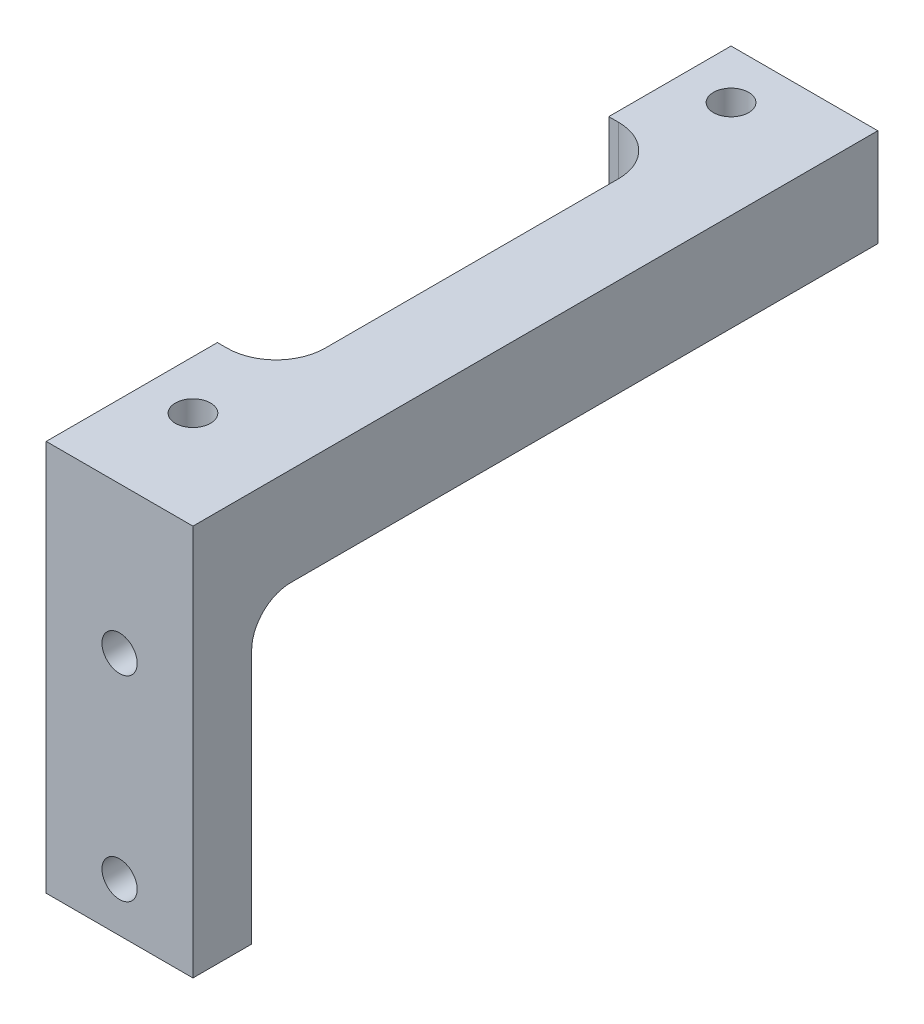
SolidWorks part; units mm, degrees
ref_plane "Front Plane" through (0, 0, 0) normal (0, 0, 1) x (1, 0, 0)
ref_plane "Top Plane" through (0, 0, 0) normal (0, 1, 0) x (1, 0, 0)
ref_plane "Right Plane" through (0, 0, 0) normal (1, 0, 0) x (0, 0, -1)
sketch "Sketch2" plane through (0, 0, 0) normal (0, 0, 1) x (1, 0, 0)
  line L1 (-23.8125, -12.7) -> (23.8125, -12.7)
  line L2 (-23.8125, -12.7) -> (-23.8125, 12.7)
  line L3 (-23.8125, 12.7) -> (23.8125, 12.7)
  line L4 (23.8125, -12.7) -> (23.8125, 12.7)
  line L5 (-23.8125, -12.7) -> (23.8125, 12.7) construction
  line L6 (-23.8125, 12.7) -> (23.8125, -12.7) construction
  point P0 (0, 0)
  dimension "D1" = 25.4
  dimension "D2" = 47.625
extrude "Boss-Extrude1" add sketch "Sketch2" along normal blind 44.45
sketch "Sketch3" plane through (0, 12.7, 0) normal (0, 1, 0) x (1, 0, 0)
  line L0 (0, 0) -> (0, -44.45) construction
  line L1 (23.8125, -44.45) -> (-23.8125, -44.45) construction
  line L2 (23.8125, 0) -> (-23.8125, 0) construction
  line L3 (-14.2875, -44.45) -> (14.2875, -44.45)
  line L4 (-14.2875, -44.45) -> (-14.2875, 0)
  line L5 (-14.2875, 0) -> (14.2875, 0)
  line L6 (14.2875, -44.45) -> (14.2875, 0)
  line L7 (-14.2875, -44.45) -> (14.2875, 0) construction
  line L8 (-14.2875, 0) -> (14.2875, -44.45) construction
  line L9 (23.8125, -44.45) -> (23.8125, 0) construction
  point P5 (0, -22.225)
  dimension "D1" = 9.525
extrude "Cut-Extrude1" cut sketch "Sketch3" against normal through all
sketch "Sketch4" plane through (-23.8125, 0, 0) normal (-1, 0, 0) x (0, 0, 1)
  line L0 (44.45, 12.7) -> (0, 12.7) construction
  line L1 (0, -12.7) -> (40.64, -12.7)
  line L2 (0, -12.7) -> (0, 6.35)
  line L3 (0, 6.35) -> (40.64, 6.35)
  line L4 (40.64, -12.7) -> (40.64, 6.35)
  line L5 (44.45, 12.7) -> (44.45, -12.7) construction
  dimension "D1" = 6.35
  dimension "D2" = 3.81
extrude "Cut-Extrude2" cut sketch "Sketch4" against normal through all
fillet "Fillet1" radius 2.54 1 edges at (19.05, 6.35, 40.64)
fillet "Fillet2" radius 2.54 1 edges at (-19.05, 6.35, 40.64)
sketch "Sketch5" plane through (0, 0, 44.45) normal (0, 0, 1) x (1, 0, 0)
  line L0 (-19.05, 12.7) -> (-19.05, -12.7) construction
  line L3 (-14.2875, 12.7) -> (-23.8125, 12.7) construction
  line L6 (-23.8125, -12.7) -> (-14.2875, -12.7) construction
  line L7 (19.05, -12.7) -> (19.05, 12.7) construction
  line L8 (14.2875, -12.7) -> (23.8125, -12.7) construction
  line L9 (23.8125, 12.7) -> (14.2875, 12.7) construction
  circle A2 centre (-19.05, -9.525) radius 1.143
  circle A3 centre (-19.05, 3.175) radius 1.143
  circle A4 centre (19.05, -9.525) radius 1.143
  circle A5 centre (19.05, 3.175) radius 1.143
  dimension "D1" = 2.286
  dimension "D2" = 2.286
  dimension "D3" = 12.7
  dimension "D4" = 3.175
  dimension "D5" = 12.7
  dimension "D6" = 3.175
  dimension "D7" = 2.286
  dimension "D8" = 2.286
extrude "Cut-Extrude3" cut sketch "Sketch5" against normal through all
sketch "Sketch6" plane through (0, 0, 44.45) normal (0, 0, 1) x (1, 0, 0)
  line L0 (19.05, -12.7) -> (19.05, 12.7) construction
  line L1 (14.2875, -12.7) -> (23.8125, -12.7) construction
  line L2 (23.8125, 12.7) -> (14.2875, 12.7) construction
  circle A1 centre (19.05, -9.525) radius 1.143
  circle A2 centre (19.05, 3.175) radius 1.143
  dimension "D1" = 12.7
  dimension "D2" = 3.175
  dimension "D3" = 2.286
  dimension "D4" = 2.286
extrude "Cut-Extrude4" cut sketch "Sketch6" against normal through all
sketch "Sketch7" plane through (0, 12.7, 0) normal (0, 1, 0) x (1, 0, 0)
  line L0 (0, 0) -> (0, -46.99) construction
  line L1 (-14.2875, 0) -> (-23.8125, 0) construction
  line L2 (-17.4625, -38.1) -> (17.4625, -38.1) construction
  line L3 (-17.4625, -38.1) -> (-17.4625, -3.175) construction
  line L4 (-17.4625, -3.175) -> (17.4625, -3.175) construction
  line L5 (17.4625, -38.1) -> (17.4625, -3.175) construction
  line L6 (-17.4625, -38.1) -> (17.4625, -3.175) construction
  line L7 (-17.4625, -3.175) -> (17.4625, -38.1) construction
  circle A1 centre (-17.4625, -38.1) radius 1.143
  circle A2 centre (17.4625, -38.1) radius 1.143
  circle A3 centre (-17.4625, -3.175) radius 1.143
  circle A4 centre (17.4625, -3.175) radius 1.143
  point P11 (0, -20.6375)
  dimension "D4" = 2.286
  dimension "D5" = 2.286
  dimension "D6" = 2.286
  dimension "D7" = 2.286
  dimension "D1" = 34.925
  dimension "D2" = 34.925
  dimension "D3" = 3.175
extrude "Cut-Extrude5" cut sketch "Sketch7" against normal blind 10.16
sketch "Sketch8" plane through (0, 12.7, 0) normal (0, 1, 0) x (1, 0, 0)
  line L0 (0, 0) -> (0, -46.99) construction
  line L1 (-17.4625, -20.6375) -> (17.4625, -20.6375) construction
  line L2 (-17.4625, -3.175) -> (17.4625, -3.175) construction
  line L3 (-17.4625, -3.175) -> (-17.4625, -38.1) construction
  line L4 (-17.4625, -38.1) -> (17.4625, -38.1) construction
  line L5 (17.4625, -3.175) -> (17.4625, -38.1) construction
  line L6 (-14.2875, 0) -> (-14.2875, -44.45) construction
  line L7 (-18.0975, -33.3375) -> (18.0975, -33.3375)
  line L8 (-18.0975, -33.3375) -> (-18.0975, -7.9375)
  line L9 (-18.0975, -7.9375) -> (18.0975, -7.9375)
  line L10 (18.0975, -33.3375) -> (18.0975, -7.9375)
  line L11 (-18.0975, -33.3375) -> (18.0975, -7.9375) construction
  line L12 (-18.0975, -7.9375) -> (18.0975, -33.3375) construction
  point P11 (0, -20.6375)
  dimension "D1" = 3.81
  dimension "D2" = 25.4
extrude "Cut-Extrude6" cut sketch "Sketch8" against normal through all
fillet "Fillet3" radius 3.175 2 edges at (-18.0975, 9.525, 7.9375) (-18.0975, 9.525, 33.3375)
fillet "Fillet4" radius 3.175 2 edges at (18.0975, 9.525, 7.9375) (18.0975, 9.525, 33.3375)
sketch "Sketch9" plane through (0, 0, 0) normal (1, 0, 0) x (0, 0, -1)
  line L1 (-46.8969, 17.6228) -> (16.8473, 17.6228)
  line L2 (-46.8969, 17.6228) -> (-46.8969, -23.6649)
  line L3 (-46.8969, -23.6649) -> (16.8473, -23.6649)
  line L4 (16.8473, 17.6228) -> (16.8473, -23.6649)
extrude "Cut-Extrude7" cut sketch "Sketch9" against normal blind 38.1
